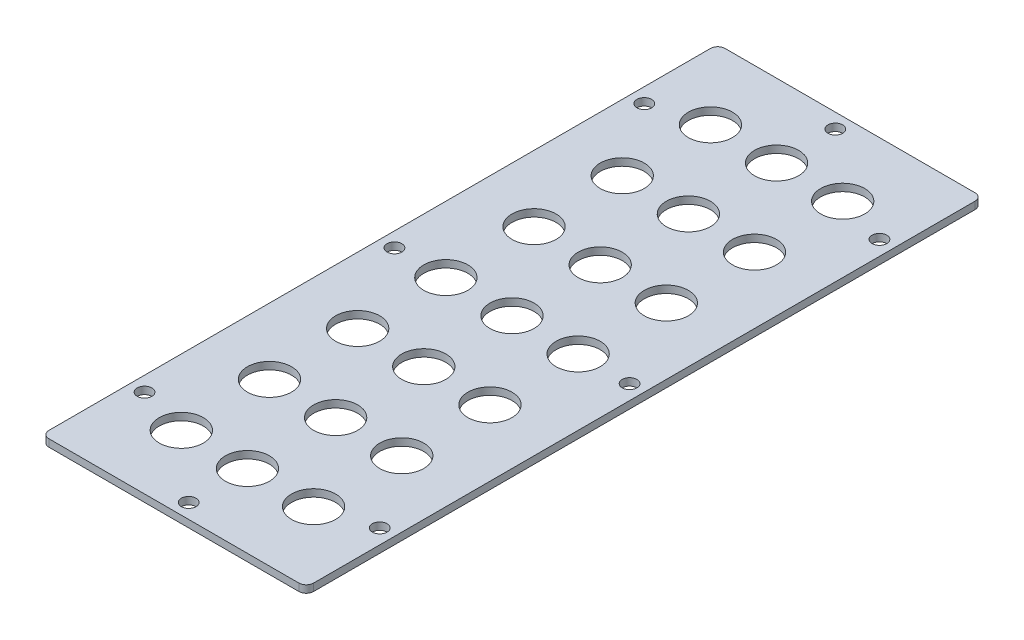
SolidWorks part; units mm, degrees
material "PC High Viscosity"
ref_plane "Front Plane" through (0, 0, 0) normal (0, 0, 1) x (1, 0, 0)
ref_plane "Top Plane" through (0, 0, 0) normal (0, 1, 0) x (1, 0, 0)
ref_plane "Right Plane" through (0, 0, 0) normal (1, 0, 0) x (0, 0, -1)
sketch "Sketch1" plane through (0, 0, 0) normal (0, 1, 0) x (1, 0, 0)
  line L1 (-57.15, -146.05) -> (57.15, -146.05)
  line L2 (-57.15, -146.05) -> (-57.15, 146.05)
  line L3 (-57.15, 146.05) -> (57.15, 146.05)
  line L4 (57.15, -146.05) -> (57.15, 146.05)
  line L5 (-57.15, -146.05) -> (57.15, 146.05) construction
  line L6 (-57.15, 146.05) -> (57.15, -146.05) construction
  point P0 (0, 0)
  dimension "D1" = 292.1
  dimension "D2" = 114.3
extrude "Boss-Extrude1" add sketch "Sketch1" along normal blind 3.175
sketch "Sketch2" plane through (0, 3.175, 0) normal (0, 1, 0) x (1, 0, 0)
  line L0 (-57.15, 114.3) -> (-28.575, 114.3) construction
  line L2 (-28.575, 114.3) -> (0, 114.3) construction
  line L3 (0, 114.3) -> (28.575, 114.3) construction
  line L4 (28.575, 114.3) -> (57.15, 114.3) construction
  circle A0 centre (-28.575, 114.3) radius 9.525
  circle A1 centre (0, 114.3) radius 9.525
  circle A2 centre (28.575, 114.3) radius 9.525
  dimension "D1" = 19.05
  dimension "D2" = 28.575
  dimension "D3" = 114.3
extrude "Cut-Extrude1" cut sketch "Sketch2" against normal through all
sketch "Sketch4" plane through (0, 3.175, 0) normal (0, 1, 0) x (1, 0, 0)
  line L0 (57.15, 146.05) -> (-57.15, 146.05) construction
  line L1 (57.15, -146.05) -> (57.15, 146.05) construction
  line L2 (-57.15, 146.05) -> (-57.15, -146.05) construction
  line L3 (-57.15, -146.05) -> (57.15, -146.05) construction
  circle A0 centre (-50.8, 0) radius 3.175
  circle A1 centre (50.8, 0) radius 3.175
  circle A2 centre (0, 139.7) radius 3.175
  circle A3 centre (0, -139.7) radius 3.175
  dimension "D5" = 6.35
  dimension "D1" = 6.35
  dimension "D2" = 6.35
  dimension "D3" = 6.35
  dimension "D4" = 6.35
extrude "Cut-Extrude2" cut sketch "Sketch4" against normal through all
pattern_linear "LPattern2" count 2 spacing 107.95 along (0, 0, -1) count 2 spacing 107.95 along (0, 0, 1) of "Cut-Extrude2"
fillet "Fillet1" radius 3.175 4 edges at (-57.15, 1.5875, -146.05) (57.15, 1.5875, -146.05) (-57.15, 1.5875, 146.05) (57.15, 1.5875, 146.05)
pattern_linear "LPattern3" count 7 spacing 38.1 along (0, 0, 1) of "Cut-Extrude1"
equation "\"D2@Sketch4\"=\"D1@Sketch4\""
equation "\"D3@Sketch4\"=\"D1@Sketch4\""
equation "\"D4@Sketch4\"=\"D1@Sketch4\""
